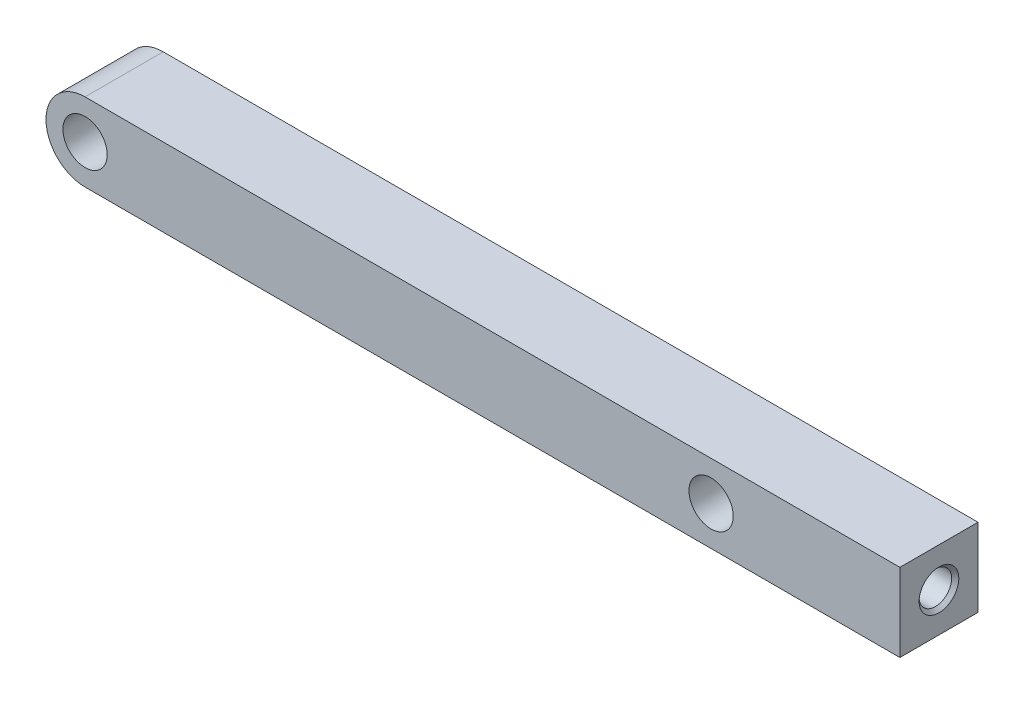
SolidWorks part; units mm, degrees
material "Delrin 2700 NC010, Low Viscosity Acetal Copolymer (SS)"
ref_plane "Front Plane" through (0, 0, 0) normal (0, 0, 1) x (1, 0, 0)
ref_plane "Top Plane" through (0, 0, 0) normal (0, 1, 0) x (1, 0, 0)
ref_plane "Right Plane" through (0, 0, 0) normal (1, 0, 0) x (0, 0, -1)
sketch "Sketch1" plane through (0, 0, 0) normal (0, 0, 1) x (1, 0, 0)
  line L0 (-24.0416, 24.0416) -> (24.0416, 24.0416) construction
  line L1 (38.5416, 27.0416) -> (-24.0416, 27.0416)
  line L2 (31.0416, 22.5416) -> (38.5416, 22.5416) construction
  line L3 (31.0416, 22.5416) -> (31.0416, 25.5416) construction
  line L4 (31.0416, 25.5416) -> (38.5416, 25.5416) construction
  line L5 (38.5416, 22.5416) -> (38.5416, 25.5416) construction
  line L6 (31.0416, 22.5416) -> (38.5416, 25.5416) construction
  line L7 (31.0416, 25.5416) -> (38.5416, 22.5416) construction
  line L8 (-24.0416, 21.0416) -> (38.5416, 21.0416)
  line L9 (38.5416, 21.0416) -> (38.5416, 27.0416)
  arc A0 (-24.0416, 27.0416) -> (-24.0416, 21.0416) centre (-24.0416, 24.0416) ccw
  point P3 (0, 24.0416)
  point P4 (34.7916, 24.0416)
  circle B0 centre (-24.0416, 24.0416) radius 1.7
  circle B1 centre (24.0416, 24.0416) radius 1.7
  circle B2 centre (24.0416, -24.0416) radius 1.7
  circle B3 centre (-24.0416, -24.0416) radius 1.7
  arc B4 (18.4243, 27.3778) -> (-18.4243, 27.3778) centre (0, 0) ccw
  arc B5 (-22.982, 26.8483) -> (-18.4243, 27.3778) centre (-21.2159, 31.526) ccw
  arc B6 (-22.982, 26.8483) -> (-26.8483, 22.982) centre (-24.0416, 24.0416) ccw
  arc B7 (-27.3778, 18.4243) -> (-26.8483, 22.982) centre (-31.526, 21.2159) ccw
  arc B8 (-27.3778, 18.4243) -> (-27.3778, -18.4243) centre (0, 0) ccw
  arc B9 (-26.8483, -22.982) -> (-27.3778, -18.4243) centre (-31.526, -21.2159) ccw
  arc B10 (-26.8483, -22.982) -> (-22.982, -26.8483) centre (-24.0416, -24.0416) ccw
  arc B11 (-18.4243, -27.3778) -> (-22.982, -26.8483) centre (-21.2159, -31.526) ccw
  arc B12 (-18.4243, -27.3778) -> (18.4243, -27.3778) centre (0, 0) ccw
  arc B13 (22.982, -26.8483) -> (18.4243, -27.3778) centre (21.2159, -31.526) ccw
  arc B14 (22.982, -26.8483) -> (26.8483, -22.982) centre (24.0416, -24.0416) ccw
  arc B15 (27.3778, -18.4243) -> (26.8483, -22.982) centre (31.526, -21.2159) ccw
  arc B16 (27.3778, -18.4243) -> (27.3778, 18.4243) centre (0, 0) ccw
  arc B17 (26.8483, 22.982) -> (27.3778, 18.4243) centre (31.526, 21.2159) ccw
  arc B18 (26.8483, 22.982) -> (22.982, 26.8483) centre (24.0416, 24.0416) ccw
  arc B19 (18.4243, 27.3778) -> (22.982, 26.8483) centre (21.2159, 31.526) ccw
  dimension "D1" = 7.5
  dimension "D2" = 3
  dimension "D3" = 4
  dimension "D4" = 3
  dimension "D5" = 3
sketch_block_instance "Block-Reaction wheel mount sketch-1"
sketch_block "Block-Reaction wheel mount sketch"
extrude "Boss-Extrude1" add sketch "Sketch1" along normal mid plane 6 contours B18 B17 L8 L9 L1 | B19 L1 B5 B6 A0 L8 B17 B18 B1 B0 | L1 B19 B18 | B6 B5 L1
hole_wizard "M3x0.5 Tapped Hole1" positions "3DSketch1" profile "Sketch2" tap size "M3x0.5" standard "ANSI Metric"
sketch3d "3DSketch1"
  line L0 (38.5416, 27.0416, 3) -> (38.5416, 27.0416, -3) construction
  line L1 (38.5416, 21.0416, 3) -> (38.5416, 27.0416, 3) construction
  point P0 (38.5416, 24.0416, 0)
  point P6 (38.5416, 27.0416, 0)
  point P9 (38.5416, 24.0416, 3)
sketch "Sketch2" plane through (38.5416, 24.0416, 0) normal (0, 1, 0) x (0, 0, -1)
  line L0 (0, 0) -> (0, 7.5)
  line L1 (0, 7.5) -> (1.25, 6.7489)
  line L2 (1.25, 6.7489) -> (1.25, 0.275)
  line L3 (1.25, 0.275) -> (1.525, 0)
  line L5 (1.525, 0) -> (0, 0)
  line L6 (-1.25, 0.275) -> (-1.525, 0) construction
  line L10 (0, 7.5) -> (-1.25, 6.7489) construction
  line L11 (0, -6.35) -> (0, 107.95) construction
  dimension "Tap Drill Dia." = 2.5
  dimension "Tap Drill Depth" = 7.5
  dimension "Near C'Sink Dia." = 3.05
  dimension "Near C'Sink Angle" = 90
  dimension "Drill Angle" = 118
cosmetic thread "Hole Thread1" parameters "D1"=6, "D2"=3
